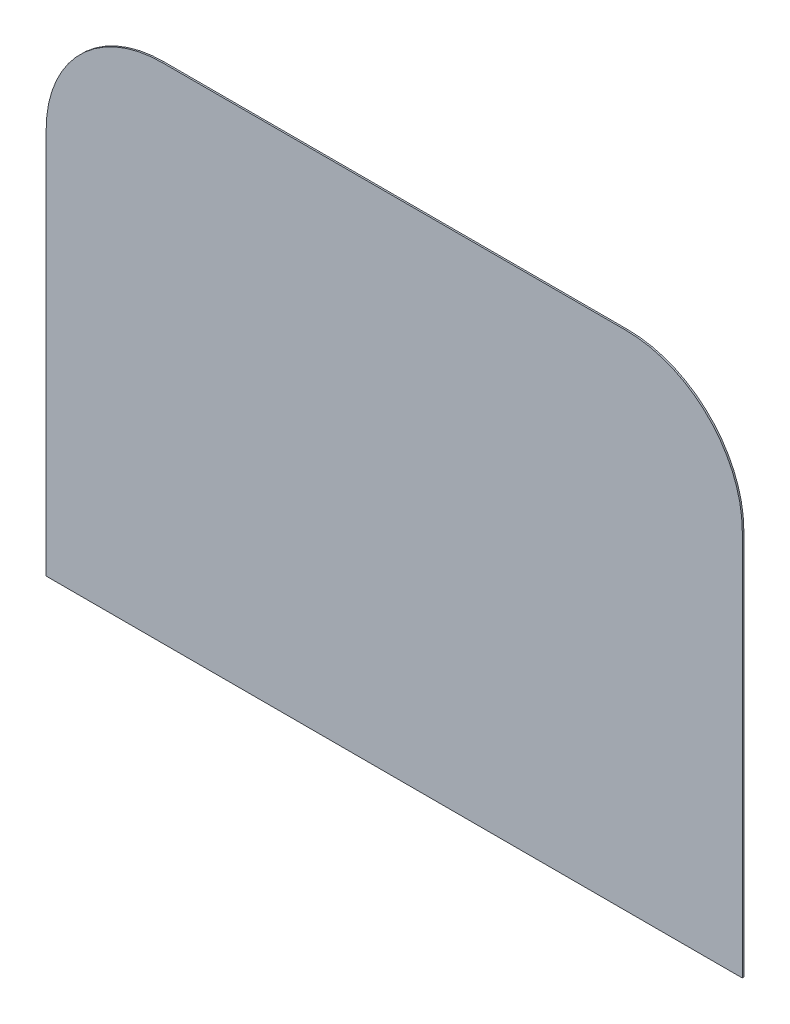
SolidWorks part; units mm, degrees
ref_plane "Спереди" through (0, 0, 0) normal (0, 0, 1) x (1, 0, 0)
ref_plane "Сверху" through (0, 0, 0) normal (0, 1, 0) x (1, 0, 0)
ref_plane "Справа" through (0, 0, 0) normal (1, 0, 0) x (0, 0, -1)
sketch "Эскиз1" plane through (0, 0, 0) normal (0, 0, 1) x (1, 0, 0)
  line L3 (-152.6491, -86.9919) -> (-152.6491, 163.0081)
  line L4 (-77.6491, 238.0081) -> (222.3509, 238.0081)
  line L5 (297.3509, 163.0081) -> (297.3509, -86.9919)
  line L6 (-152.6491, -86.9919) -> (272.3509, -86.9919)
  line L7 (272.3509, -86.9919) -> (297.3509, -86.9919)
  arc A2 (-152.6491, 163.0081) -> (-77.6491, 238.0081) centre (-77.6491, 163.0081) cw
  arc A3 (222.3509, 238.0081) -> (297.3509, 163.0081) centre (222.3509, 163.0081) cw
extrude "Бобышка-Вытянуть2" add sketch "Эскиз1" along normal blind 1
